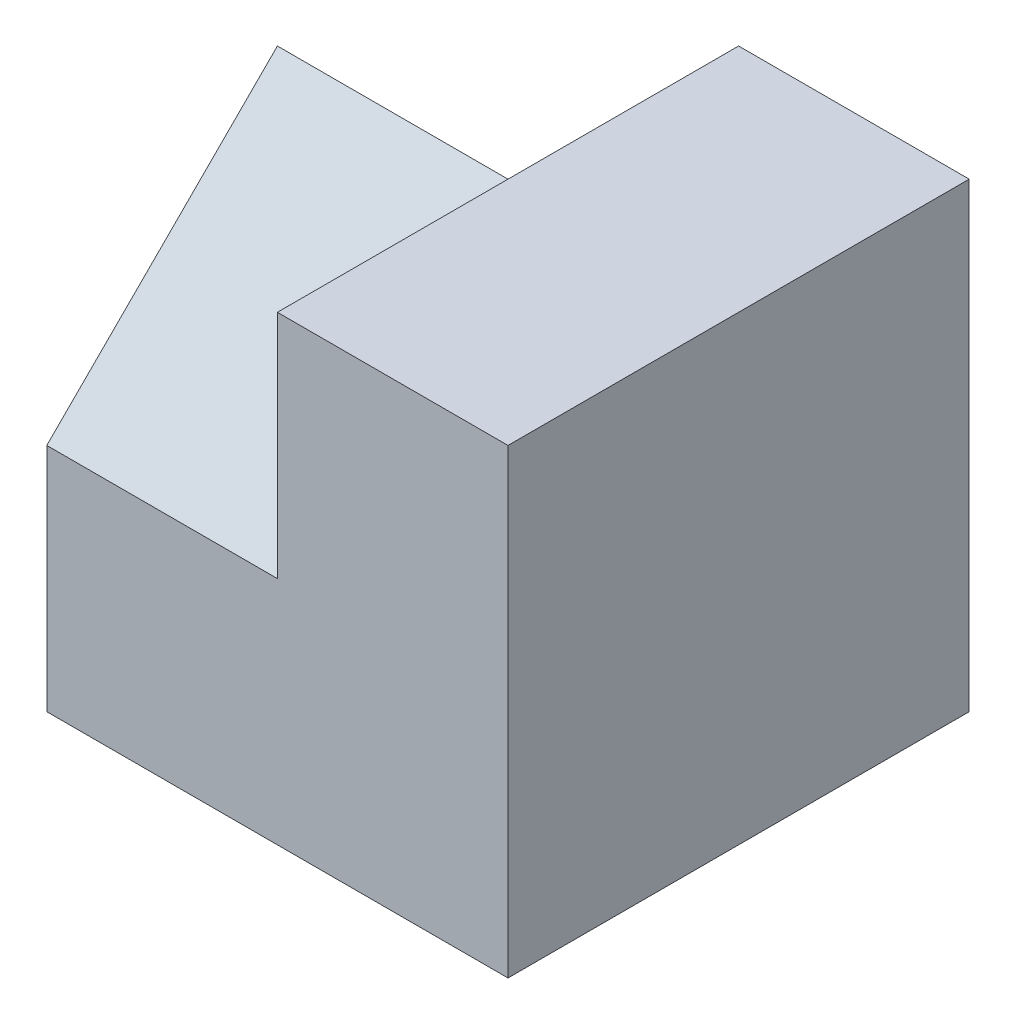
SolidWorks part; units mm, degrees
ref_plane "Front" through (0, 0, 0) normal (0, 0, 1) x (1, 0, 0)
ref_plane "Top" through (0, 0, 0) normal (0, 1, 0) x (1, 0, 0)
ref_plane "Right" through (0, 0, 0) normal (1, 0, 0) x (0, 0, -1)
sketch "Sketch1" plane through (0, 0, 0) normal (0, 1, 0) x (1, 0, 0)
  line L1 (-2, -2) -> (2, -2)
  line L2 (-2, -2) -> (-2, 2)
  line L3 (-2, 2) -> (2, 2)
  line L4 (2, -2) -> (2, 2)
  line L5 (-2, -2) -> (2, 2) construction
  line L6 (-2, 2) -> (2, -2) construction
  point P0 (0, 0)
  dimension "D1" = 4
  dimension "D2" = 4
extrude "Boss-Extrude1" add sketch "Sketch1" along normal blind 4
sketch "Sketch2" plane through (-2, 0, 0) normal (-1, 0, 0) x (0, 0, 1)
  line L0 (2, 2) -> (0, 4)
  line L1 (2, 4) -> (2, 0) construction
  line L2 (-2, 4) -> (2, 4) construction
  line L3 (0, 4) -> (-2, 2)
  line L4 (-2, 4) -> (-2, 0) construction
  line L5 (-2, 2) -> (0, 0)
  line L9 (-2, 0) -> (2, 0)
  line L10 (2, 0) -> (2, 4)
  line L11 (2, 4) -> (-2, 4)
  line L12 (-2, 4) -> (-2, 0)
  line L13 (-2, 0) -> (2, 0)
  line L14 (2, 0) -> (2, 4)
  line L15 (2, 4) -> (-2, 4)
  line L16 (-2, 4) -> (-2, 0)
  line M5 (-2, 0) -> (2, 0)
  line M6 (2, 0) -> (2, 4)
  line M7 (2, 4) -> (-2, 4)
  line M8 (-2, 4) -> (-2, 0)
  dimension "D1" = 0
extrude "Cut-Extrude1" cut sketch "Sketch2" against normal blind 2 contours L0 M6 M7 | L5 M8 M5 | L3 M7 M8 | L13 L14 L15 L16
